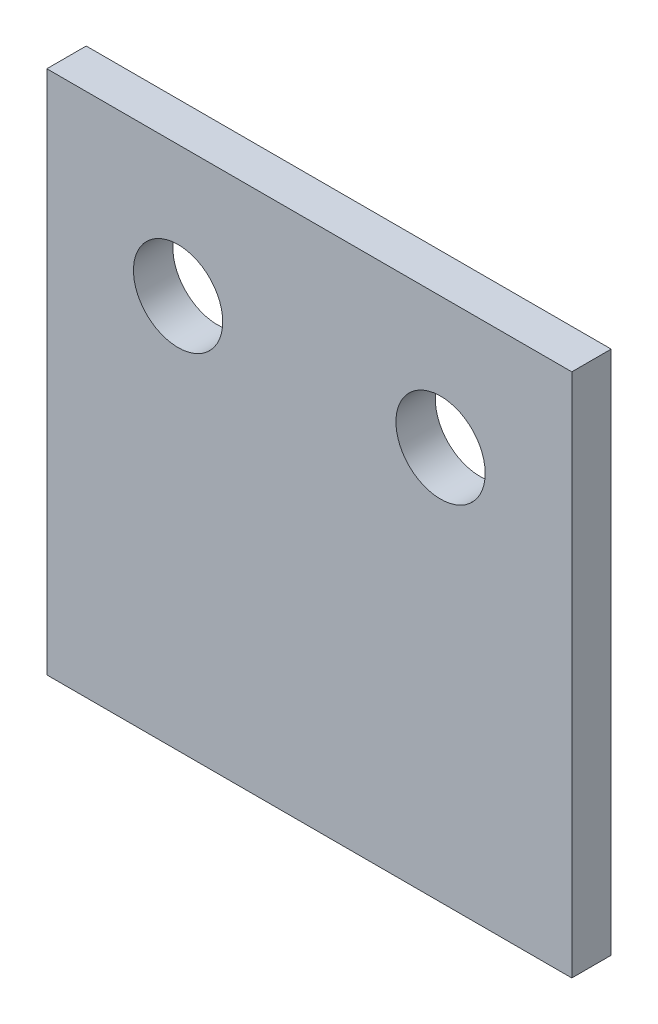
SolidWorks part; units mm, degrees
ref_plane "Plan de face" through (0, 0, 0) normal (0, 0, 1) x (1, 0, 0)
ref_plane "Plan de dessus" through (0, 0, 0) normal (0, 1, 0) x (1, 0, 0)
ref_plane "Plan de droite" through (0, 0, 0) normal (1, 0, 0) x (0, 0, -1)
sketch "Esquisse1" plane through (0, 0, 0) normal (0, 0, 1) x (1, 0, 0)
  line L1 (0, 0) -> (20, 0)
  line L2 (0, 0) -> (0, 20)
  line L3 (0, 20) -> (20, 20)
  line L4 (20, 0) -> (20, 20)
  dimension "D1" = 20
  dimension "D2" = 20
extrude "Boss.-Extru.2" add sketch "Esquisse1" along normal blind 1.5
sketch "Esquisse2" plane through (0, 0, 1.5) normal (0, 0, 1) x (1, 0, 0)
  line L0 (20, 0) -> (20, 20) construction
  line L1 (20, 20) -> (0, 20) construction
  line L2 (20, 15) -> (0, 15) construction
  line L3 (0, 20) -> (0, 0) construction
  line L4 (15, 20) -> (15, 13.6781) construction
  line L5 (5, 20) -> (5, 9.0647) construction
  point P0 (20, 15)
  point P1 (15, 20)
  point P13 (5, 20)
  point P17 (5, 15)
  point P18 (15, 15)
  dimension "D1" = 5
  dimension "D2" = 5
  dimension "D3" = 5
hole_wizard "Dégagement M31" positions "Esquisse3D1" profile "Esquisse3" hole size "M3" standard "ISO" end condition through all
sketch3d "Esquisse3D1"
  point P0 (5, 15, 1.5)
  point P3 (15, 15, 1.5)
sketch "Esquisse3" plane through (5, 15, 1.5) normal (1, 0, 0) x (0, -1, 0)
  line L0 (0, 0) -> (0, 1.5)
  line L1 (0, 1.5) -> (1.7, 1.5)
  line L2 (1.7, 1.5) -> (1.7, 0)
  line L5 (1.7, 0) -> (0, 0)
  line L11 (0, -6.35) -> (0, 107.95) construction
  dimension "Diamètre du perçage jusqu'au prochain" = 3.4
  dimension "Profondeur du perçage jusqu'au prochain" = 1.5
